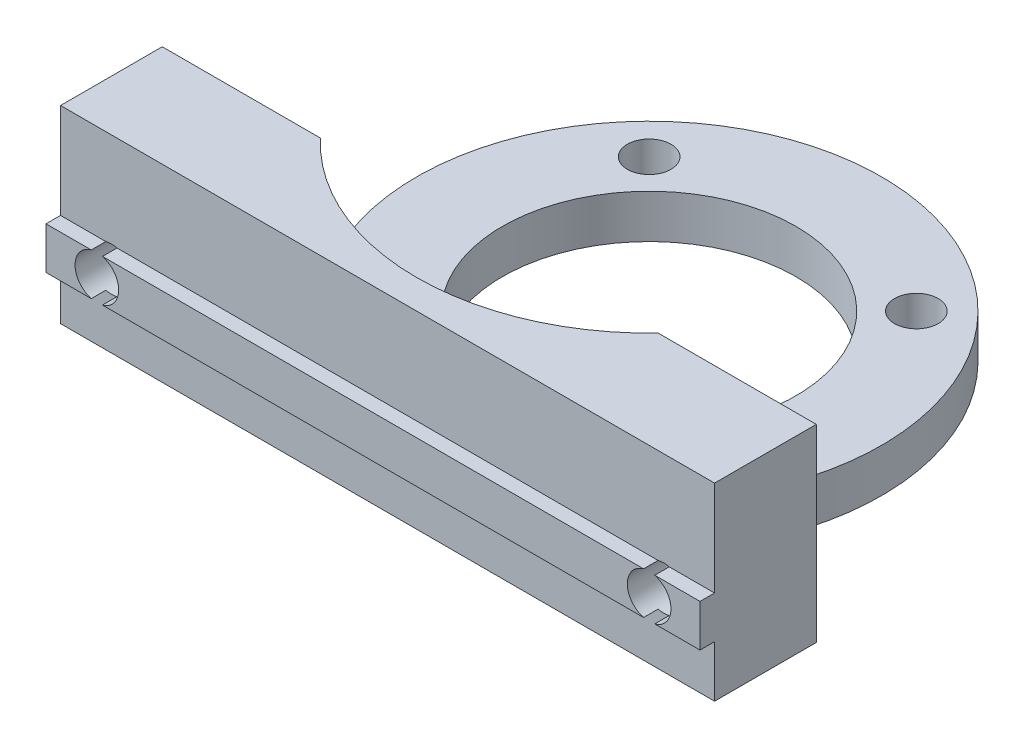
SolidWorks part; units mm, degrees
ref_plane "Front Plane" through (0, 0, 0) normal (0, 0, 1) x (1, 0, 0)
ref_plane "Top Plane" through (0, 0, 0) normal (0, 1, 0) x (1, 0, 0)
ref_plane "Right Plane" through (0, 0, 0) normal (1, 0, 0) x (0, 0, -1)
sketch "Sketch1" plane through (0, 0, 0) normal (0, 0, 1) x (1, 0, 0)
  line L1 (-22.5, -6.5) -> (22.5, -6.5)
  line L2 (-22.5, -6.5) -> (-22.5, 6.5)
  line L3 (-22.5, 6.5) -> (22.5, 6.5)
  line L4 (22.5, -6.5) -> (22.5, 6.5)
  line L5 (-22.5, -6.5) -> (22.5, 6.5) construction
  line L6 (-22.5, 6.5) -> (22.5, -6.5) construction
  point P0 (0, 0)
  dimension "D1" = 45
  dimension "D2" = 13
extrude "Main" add sketch "Sketch1" along normal blind 7
sketch "Sketch4" plane through (0, 0, 7) normal (0, 0, 1) x (1, 0, 0)
  line L0 (-22.5, 6.5) -> (-22.5, -6.5) construction
  line L1 (-22.5, -2.95) -> (22.5, -2.95)
  line L2 (-22.5, -2.95) -> (-22.5, -0.05)
  line L3 (-22.5, -0.05) -> (22.5, -0.05)
  line L4 (22.5, -2.95) -> (22.5, -0.05)
  line L5 (22.5, -6.5) -> (22.5, 6.5) construction
  line L7 (-22.5, -6.5) -> (22.5, -6.5) construction
  dimension "D1" = 2.9
  dimension "D2" = 3.55
extrude "MakerBeamFix" add sketch "Sketch4" along normal blind 1
sketch "Sketch5" plane through (0, 0, 8) normal (0, 0, 1) x (1, 0, 0)
  line L0 (-22.5, -0.05) -> (-22.5, -2.95) construction
  line L1 (-19, -1.5) -> (19, -1.5) construction
  circle A0 centre (-19, -1.5) radius 1.5
  circle A1 centre (19, -1.5) radius 1.5
  point P4 (0, -1.5)
  point P6 (15, 1.7066)
  point P7 (-22.5, -1.5)
  point P8 (0, 0)
  dimension "D1" = 38
  dimension "D3" = 3
extrude "MakerBeamHole" cut sketch "Sketch5" against normal through all
sketch "Sketch6" plane through (0, -6.5, 0) normal (0, 1, 0) x (1, 0, 0)
  line L0 (22.5, -7) -> (19.3841, -7) construction
  circle A0 centre (0, 11) radius 16
  circle A1 centre (0, 11) radius 10.1
  point P3 (0, 0)
  point P7 (20.942, -7)
  dimension "D1" = 20.2
  dimension "D2" = 32
  dimension "D3" = 18
extrude "MotorFix" add sketch "Sketch6" along normal blind 3
sketch "Sketch7" plane through (0, 6.5, 0) normal (0, -1, 0) x (-1, 0, 0)
  circle A0 centre (0, 11) radius 16
  circle A1 centre (0, 11) radius 16 construction
extrude "MotorHole" cut sketch "Sketch7" against normal up to surface (10 mm away)
sketch "Sketch8" plane through (0, 6.5, 0) normal (0, 1, 0) x (1, 0, 0)
  line L1 (-9.1924, 20.1924) -> (9.1924, 20.1924) construction
  line L2 (-9.1924, 20.1924) -> (-9.1924, 1.8076) construction
  line L3 (-9.1924, 1.8076) -> (9.1924, 1.8076) construction
  line L4 (9.1924, 20.1924) -> (9.1924, 1.8076) construction
  circle A0 centre (0, 11) radius 13 construction
  circle A1 centre (9.1924, 20.1924) radius 1.5
  circle A2 centre (-9.1924, 20.1924) radius 1.5
  circle A3 centre (-9.1924, 1.8076) radius 1.5
  circle A4 centre (9.1924, 1.8076) radius 1.5
  point P11 (0, 0)
  point P12 (9.0035, 20.3775)
  point P14 (-9.3768, 1.3289)
  dimension "D1" = 26
  dimension "D2" = 3
extrude "MotorFixHole" cut sketch "Sketch8" against normal through all
fillet "Fillet1" radius 3 2 edges at (11.619, -5, 0) (-11.619, -5, 0)
